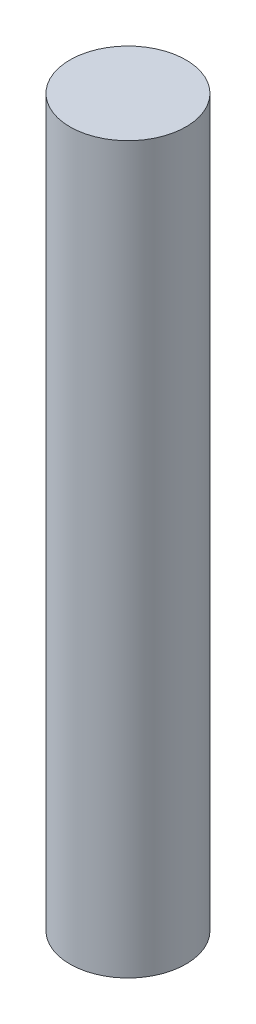
SolidWorks part; units mm, degrees
ref_plane "Front Plane" through (0, 0, 0) normal (0, 0, 1) x (1, 0, 0)
ref_plane "Top Plane" through (0, 0, 0) normal (0, 1, 0) x (1, 0, 0)
ref_plane "Right Plane" through (0, 0, 0) normal (1, 0, 0) x (0, 0, -1)
sketch "Sketch1" plane through (0, 0, 0) normal (0, 1, 0) x (1, 0, 0)
  circle A0 centre (0, 0) radius 16
  dimension "D1" = 32
extrude "Boss-Extrude1" add sketch "Sketch1" along normal blind 200
